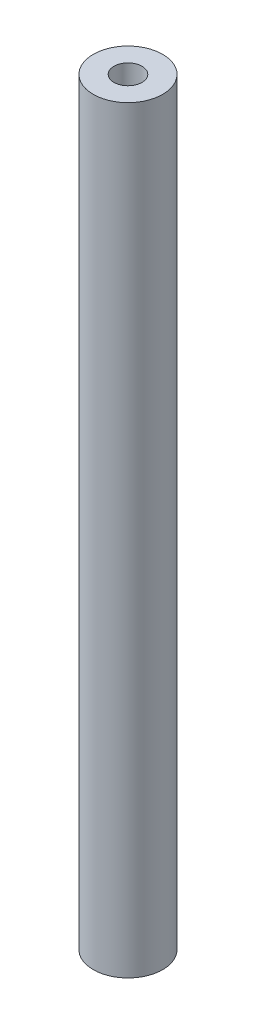
SolidWorks part; units mm, degrees
material "AISI 316 Annealed Stainless Steel Bar (SS)"
ref_plane "Front Plane" through (0, 0, 0) normal (0, 0, 1) x (1, 0, 0)
ref_plane "Top Plane" through (0, 0, 0) normal (0, 1, 0) x (1, 0, 0)
ref_plane "Right Plane" through (0, 0, 0) normal (1, 0, 0) x (0, 0, -1)
sketch "Sketch1" plane through (0, 0, 0) normal (0, 1, 0) x (1, 0, 0)
  circle A0 centre (0, 0) radius 5
  dimension "D1" = 10
extrude "Boss-Extrude2" add sketch "Sketch1" against normal blind 109.22
ref_plane "Plane1" through (0, 0, -5) normal (0, 0, -1) x (-1, 0, 0)
sketch "Sketch2" plane through (0, 0, -5) normal (0, 0, -1) x (-1, 0, 0)
  line L0 (0, -10.39) -> (0, -15.39) construction
  line L1 (0, -109.22) -> (0, 0) construction
  line L2 (1.5, -10.39) -> (1.5, -15.39)
  line L3 (-1.5, -10.39) -> (-1.5, -15.39)
  line L5 (0, -63.5) -> (0, -68.5) construction
  line L6 (1.5, -63.5) -> (1.5, -68.5)
  line L7 (-1.5, -63.5) -> (-1.5, -68.5)
  line L8 (5, 0) -> (-5, 0) construction
  line L9 (0, -109.22) -> (0, -114.22) construction
  line L10 (2, -109.22) -> (2, -114.22)
  line L11 (-2, -109.22) -> (-2, -114.22)
  arc A0 (1.5, -10.39) -> (-1.5, -10.39) centre (0, -10.39) ccw
  arc A1 (-1.5, -15.39) -> (1.5, -15.39) centre (0, -15.39) ccw
  arc A2 (1.5, -63.5) -> (-1.5, -63.5) centre (0, -63.5) ccw
  arc A3 (-1.5, -68.5) -> (1.5, -68.5) centre (0, -68.5) ccw
  arc A4 (2, -109.22) -> (-2, -109.22) centre (0, -109.22) ccw
  arc A5 (-2, -114.22) -> (2, -114.22) centre (0, -114.22) ccw
  point P5 (0, -12.89)
  point P10 (0, -8.89)
  point P11 (0, -16.89)
  point P14 (0, -66)
  point P19 (0, -111.72)
  dimension "D2" = 8
  dimension "D5" = 109.22
  dimension "D1" = 3
  dimension "D3" = 8.89
  dimension "D4" = 63.5
  dimension "D6" = 4
extrude "Cut-Extrude1" cut sketch "Sketch2" against normal blind 2.54 contours L11 A5 L10 A4 | L7 A3 L6 A2 | L3 A1 L2 A0
hole_wizard "Tap Drill for #10-32 Tap1" positions "3DSketch1" profile "Sketch3" hole size "#10-32" standard "ANSI Inch"
sketch3d "3DSketch1"
  line L0 (0, -109.22, 0) -> (0, 0, 0) construction
  circle A0 centre (0, 0, 0) radius 5 construction
  point P0 (0, 0, 0)
  point P3 (0, -109.22, 0)
  point P7 (0, 0, 0)
  point P9 (0, 0, 0)
  point P14 (0, 5, 0)
sketch "Sketch3" plane through (0, 0, 0) normal (1, 0, 0) x (0, 0, 1)
  line L0 (0, 0) -> (0, 12.7)
  line L1 (0, 12.7) -> (2.0193, 11.4867)
  line L2 (2.0193, 11.4867) -> (2.0193, 0)
  line L5 (2.0193, 0) -> (0, 0)
  line L10 (0, 12.7) -> (-2.0193, 11.4867) construction
  line L11 (0, -6.35) -> (0, 107.95) construction
  dimension "Hole Dia." = 4.0386
  dimension "Hole Depth" = 12.7
  dimension "Drill Angle" = 118
